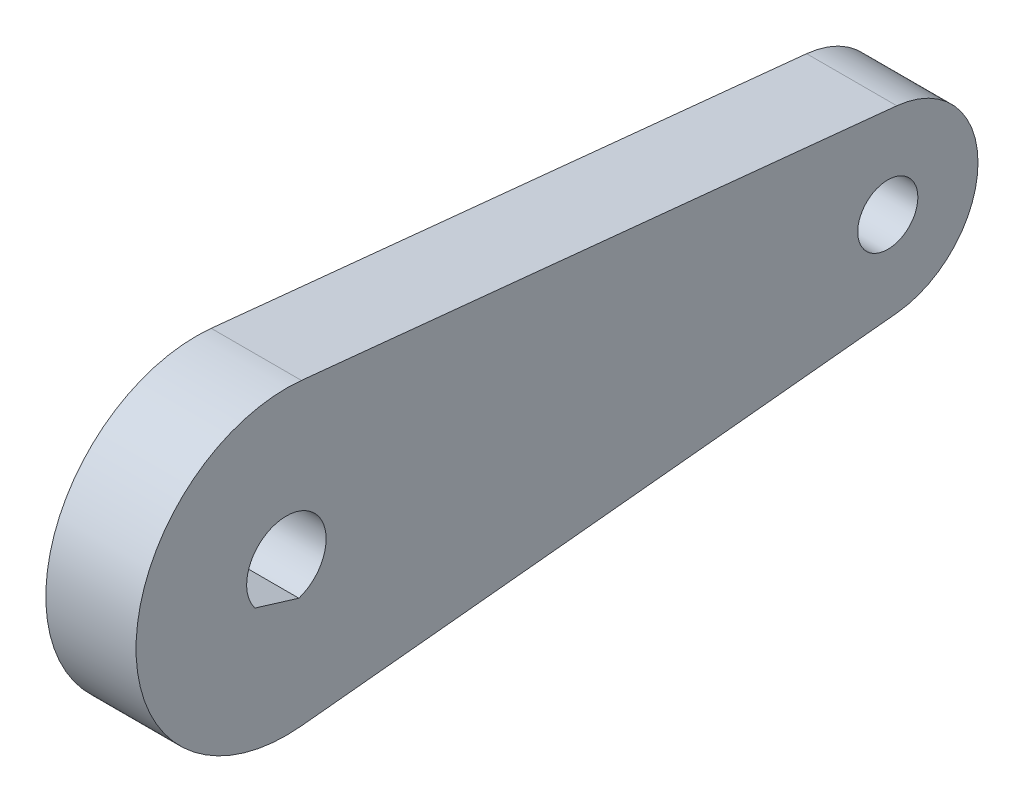
SolidWorks part; units mm, degrees
ref_plane "Front Plane" through (0, 0, 0) normal (0, 0, 1) x (1, 0, 0)
ref_plane "Top Plane" through (0, 0, 0) normal (0, 1, 0) x (1, 0, 0)
ref_plane "Right Plane" through (0, 0, 0) normal (1, 0, 0) x (0, 0, -1)
sketch "Sketch1" plane through (0, 0, 0) normal (1, 0, 0) x (0, 0, -1)
  line L0 (40.6, -5.9699) -> (1, -9.9499) construction
  line L1 (40.6, 5.9699) -> (1, 9.9499) construction
  line L2 (40.6, -5.9699) -> (1, -9.9499)
  line L3 (40.6, 5.9699) -> (1, 9.9499)
  circle A1 centre (40, 0) radius 6
  circle A2 centre (40, 0) radius 6
  circle A3 centre (0, 0) radius 10
  circle A4 centre (0, 0) radius 10
  dimension "D1" = 0
  dimension "D2" = 0
extrude "Boss-Extrude1" add sketch "Sketch1" along normal up to surface (3 mm away) and the other way up to surface (3 mm away) contours A4 | A4 L2 A2 L3 | A2
sketch "Sketch2" plane through (0, 0, 0) normal (1, 0, 0) x (0, 0, -1)
  circle A0 centre (40, 0) radius 2 construction
  circle A1 centre (40, 0) radius 2
extrude "Cut-Extrude1" cut sketch "Sketch2" against normal through all both and the other way through all
sketch "Sketch3" plane through (3, 0, 0) normal (1, 0, 0) x (0, 0, -1)
  line L0 (-2.0011, -1.4868) -> (0.8273, -2.3517) construction
  line L1 (-2.0914, -1.6161) -> (0.8298, -2.5094)
  arc A0 (0.8273, -2.3517) -> (-2.0011, -1.4868) centre (0, 0) ccw construction
  arc A1 (0.8273, -2.3517) -> (-2.0011, -1.4868) centre (0, 0) ccw construction
  arc A2 (0.8298, -2.5094) -> (-2.0914, -1.6161) centre (0, 0) ccw
  point P3 (0, 0)
  point P5 (-1.9755, -1.4868)
  dimension "D1" = 0.15
extrude "Cut-Extrude2" cut sketch "Sketch3" against normal blind 10
